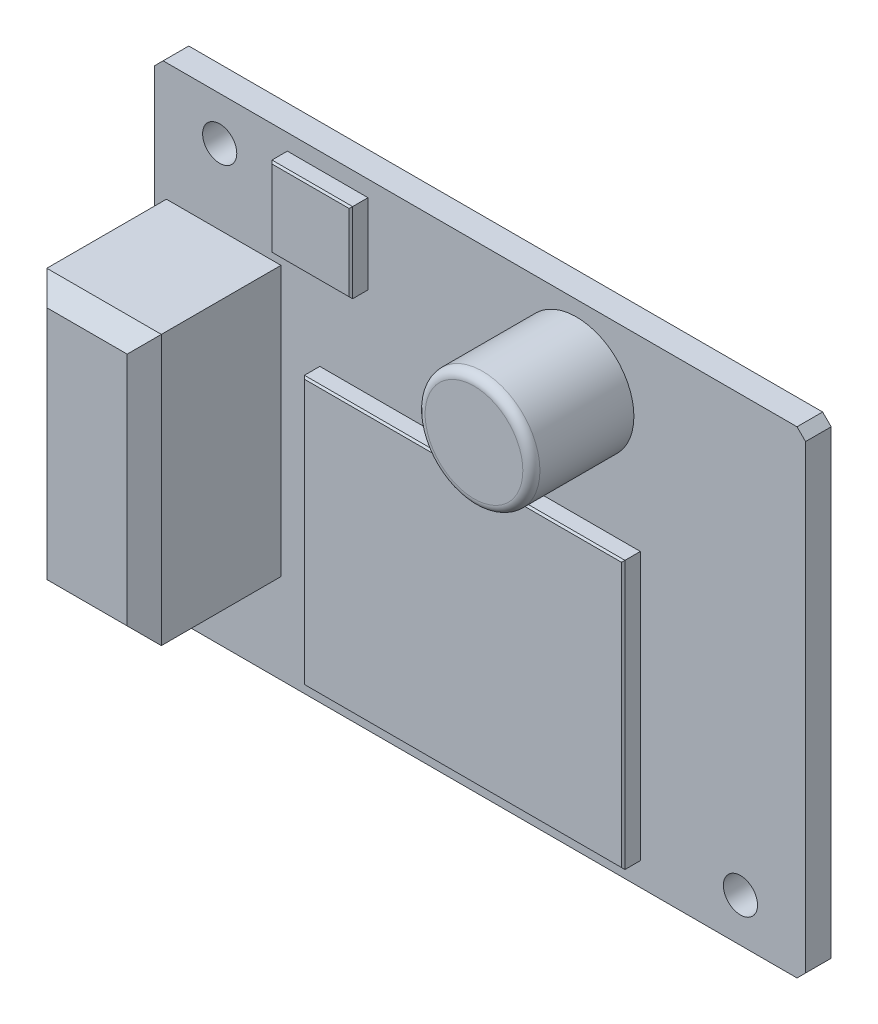
SolidWorks part; units mm, degrees
ref_plane "Front Plane" through (0, 0, 0) normal (0, 0, 1) x (1, 0, 0)
ref_plane "Top Plane" through (0, 0, 0) normal (0, 1, 0) x (1, 0, 0)
ref_plane "Right Plane" through (0, 0, 0) normal (1, 0, 0) x (0, 0, -1)
sketch "Sketch1" plane through (0, 0, 0) normal (0, 0, 1) x (1, 0, 0)
  line L0 (-15.24, 11.43) -> (15.24, -11.43) construction
  line L1 (19.05, -13.97) -> (-19.05, -13.97)
  line L2 (19.05, -13.97) -> (19.05, 13.97)
  line L3 (19.05, 13.97) -> (-19.05, 13.97)
  line L4 (-19.05, -13.97) -> (-19.05, 13.97)
  line L5 (19.05, -13.97) -> (-19.05, 13.97) construction
  line L6 (19.05, 13.97) -> (-19.05, -13.97) construction
  circle A4 centre (-15.24, 11.43) radius 1
  circle A5 centre (15.24, -11.43) radius 1
  point P0 (0, 0)
  point P10 (-26.3288, 19.3078)
  point P11 (0, 0)
  point P12 (-27.7155, 11.43)
  dimension "D5" = 2
  dimension "D4" = 30.48
  dimension "D1" = 27.94
  dimension "D2" = 38.1
  dimension "D3" = 22.86
extrude "Boss-Extrude1" add sketch "Sketch1" along normal blind 1.5
chamfer "Chamfer1" distance 0.5 angle 45 4 edges at (19.05, -13.97, 0.75) (-19.05, -13.97, 0.75) (-19.05, 13.97, 0.75) (19.05, 13.97, 0.75)
sketch "Sketch2" plane through (0, 0, 1.5) normal (0, 0, 1) x (1, 0, 0)
  line L1 (9.3793, -12.6073) -> (-9.3793, -12.6073)
  line L2 (9.3793, -12.6073) -> (9.3793, 3.0655)
  line L3 (9.3793, 3.0655) -> (-9.3793, 3.0655)
  line L4 (-9.3793, -12.6073) -> (-9.3793, 3.0655)
  line L5 (9.3793, -12.6073) -> (-9.3793, 3.0655) construction
  line L6 (9.3793, 3.0655) -> (-9.3793, -12.6073) construction
  line L7 (-11.279, 13.0265) -> (-6.5593, 13.0265)
  line L8 (-11.279, 13.0265) -> (-11.279, 8.3525)
  line L9 (-11.279, 8.3525) -> (-6.5593, 8.3525)
  line L10 (-6.5593, 13.0265) -> (-6.5593, 8.3525)
  line L11 (-11.279, 13.0265) -> (-6.5593, 8.3525) construction
  line L12 (-11.279, 8.3525) -> (-6.5593, 13.0265) construction
  point P0 (0, -4.7709)
  point P5 (-8.9192, 10.6895)
  point P10 (-8.9192, 10.6895)
extrude "Boss-Extrude2" add sketch "Sketch2" along normal blind 1
sketch "Sketch3" plane through (0, 0, 1.5) normal (0, 0, 1) x (1, 0, 0)
  circle A0 centre (5.6438, 9.7245) radius 3.3593
extrude "Boss-Extrude3" add sketch "Sketch3" along normal blind 6
chamfer "Chamfer2" distance 0.1 angle 45 8 edges at (0, 3.0655, 2.5) (9.3793, -4.7709, 2.5) (0, -12.6073, 2.5) (-9.3793, -4.7709, 2.5) (-8.9192, 8.3525, 2.5) (-11.279, 10.6895, 2.5) (-8.9192, 13.0265, 2.5) (-6.5593, 10.6895, 2.5)
fillet "Fillet1" radius 0.5 1 edges at (9.0031, 9.7245, 7.5)
sketch "Sketch4" plane through (0, 0, 1.5) normal (0, 0, 1) x (1, 0, 0)
  line L1 (-18.3576, 7.0509) -> (-11.6541, 7.0509)
  line L2 (-18.3576, 7.0509) -> (-18.3576, -8.7268)
  line L3 (-18.3576, -8.7268) -> (-11.6541, -8.7268)
  line L4 (-11.6541, 7.0509) -> (-11.6541, -8.7268)
  line L5 (-18.3576, 7.0509) -> (-11.6541, -8.7268) construction
  line L6 (-18.3576, -8.7268) -> (-11.6541, 7.0509) construction
  point P0 (-15.0058, -0.8379)
extrude "Boss-Extrude4" add sketch "Sketch4" along normal blind 8
chamfer "Chamfer3" distance 1 angle 45 4 edges at (-15.0058, -8.7268, 9.5) (-18.3576, -0.8379, 9.5) (-15.0058, 7.0509, 9.5) (-11.6541, -0.8379, 9.5)
equation "\"1.2i\"=30.48"
